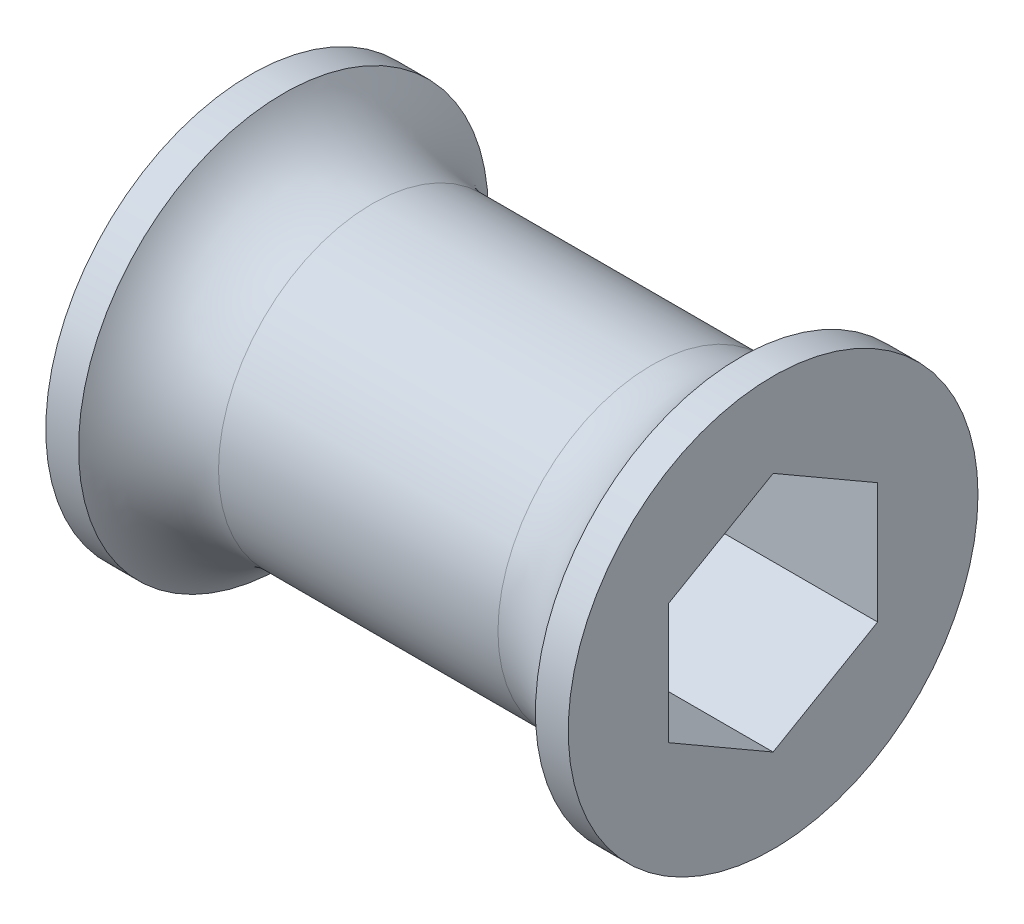
SolidWorks part; units mm, degrees
ref_plane "Front" through (0, 0, 0) normal (0, 0, 1) x (1, 0, 0)
ref_plane "Top" through (0, 0, 0) normal (0, 1, 0) x (1, 0, 0)
ref_plane "Right" through (0, 0, 0) normal (1, 0, 0) x (0, 0, -1)
sketch "Sketch1" plane through (0, 0, 0) normal (0, 0, 1) x (1, 0, 0)
  line L0 (0, 0) -> (0, 12.7)
  line L1 (0, 12.7) -> (2.032, 12.7)
  line L2 (0, 0) -> (32.385, 0)
  line L3 (32.385, 0) -> (32.385, 12.7)
  line L4 (32.385, 12.7) -> (30.353, 12.7)
  line L5 (7.5313, 9.525) -> (24.8537, 9.525)
  line L6 (0, 0) -> (-4.8272, 0) construction
  arc A0 (24.8537, 9.525) -> (30.353, 12.7) centre (24.8537, 15.875) ccw
  arc A1 (7.5313, 9.525) -> (2.032, 12.7) centre (7.5313, 15.875) cw
  dimension "D6" = 6.35
  dimension "D1" = 25.4
  dimension "D4" = 2.032
  dimension "D5" = 19.05
  dimension "D7" = 32.385
revolve "Revolve1" add sketch "Sketch1" angle 360 about L6
sketch "Sketch2" plane through (0, 0, 0) normal (-1, 0, 0) x (0, 0, 1)
  line L1 (0, 7.479) -> (-6.477, 3.7395)
  line L2 (-6.477, 3.7395) -> (-6.477, -3.7395)
  line L3 (-6.477, -3.7395) -> (0, -7.479)
  line L4 (0, -7.479) -> (6.477, -3.7395)
  line L5 (6.477, -3.7395) -> (6.477, 3.7395)
  line L6 (6.477, 3.7395) -> (0, 7.479)
  circle A0 centre (0, 0) radius 6.477 construction
  dimension "D1" = 12.954
extrude "Cut-Extrude1" cut sketch "Sketch2" against normal through all
